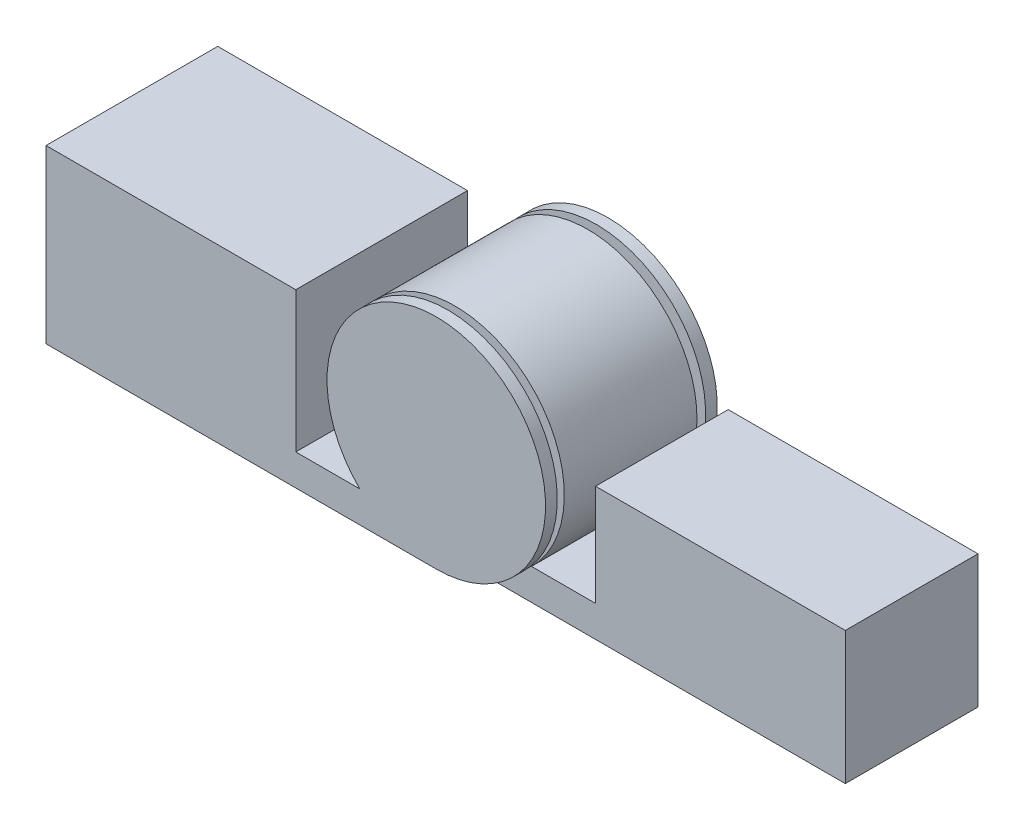
SolidWorks part; units mm, degrees
ref_plane "Front Plane" through (0, 0, 0) normal (0, 0, 1) x (1, 0, 0)
ref_plane "Top Plane" through (0, 0, 0) normal (0, 1, 0) x (1, 0, 0)
ref_plane "Right Plane" through (0, 0, 0) normal (1, 0, 0) x (0, 0, -1)
sketch "Sketch1" plane through (0, 0, 0) normal (0, 0, 1) x (1, 0, 0)
  line L0 (203.2, 0) -> (317.5, 0)
  line L1 (0, 0) -> (203.2, 0)
  line L2 (0, 0) -> (0, 139.7)
  line L3 (0, 139.7) -> (203.2, 139.7)
  line L4 (203.2, 25.4) -> (203.2, 139.7)
  line L5 (203.2, 25.4) -> (255.283, 25.4)
  arc A0 (317.5, 0) -> (255.283, 25.4) centre (317.5, 88.9) ccw
  dimension "D3" = 177.8
  dimension "D1" = 139.7
  dimension "D2" = 203.2
  dimension "D4" = 25.4
  dimension "D5" = 114.3
  dimension "D6" = 203.2
extrude "Boss-Extrude1" add sketch "Sketch1" along normal blind 139.7 contours L3 L4 L5 A0 L0 L1 L2
ref_plane "Plane1" through (0, 0, 69.85) normal (0, 0, 1) x (1, 0, 0)
sketch "Sketch3" plane through (0, 0, 69.85) normal (0, 0, 1) x (1, 0, 0)
  circle A0 centre (317.5, 88.9) radius 88.9
  arc A1 (317.5, 0) -> (255.283, 25.4) centre (317.5, 88.9) ccw construction
  dimension "D1" = 177.8
extrude "Cut-Extrude1" cut sketch "Sketch3" along normal offset from surface 9.525 and the other way offset from surface (60.325 mm away) 9.525 up to face at (173.9821, 81.4509, 139.7) other way up to face at (173.9821, 81.4509, 0)
sketch "Sketch2" plane through (0, 0, 0) normal (0, 0, 1) x (1, 0, 0)
  line L1 (317.5, 0) -> (431.8, 0)
  line L3 (379.717, 25.4) -> (431.8, 25.4)
  line L5 (431.8, 0) -> (635, 0)
  line L6 (431.8, 25.4) -> (431.8, 107.95)
  line L7 (431.8, 107.95) -> (635, 107.95)
  line L8 (635, 0) -> (635, 107.95)
  arc A0 (379.717, 25.4) -> (317.5, 0) centre (317.5, 88.9) ccw
  arc A1 (317.5, 0) -> (255.283, 25.4) centre (317.5, 88.9) ccw construction
  dimension "D2" = 114.3
  dimension "D1" = 88.9
  dimension "D3" = 25.4
  dimension "D4" = 203.2
  dimension "D5" = 107.95
extrude "Boss-Extrude2" add sketch "Sketch2" along normal blind 107.95 from offset 16.51 contours L7 L8 L5 L1 A0 L3 L6
